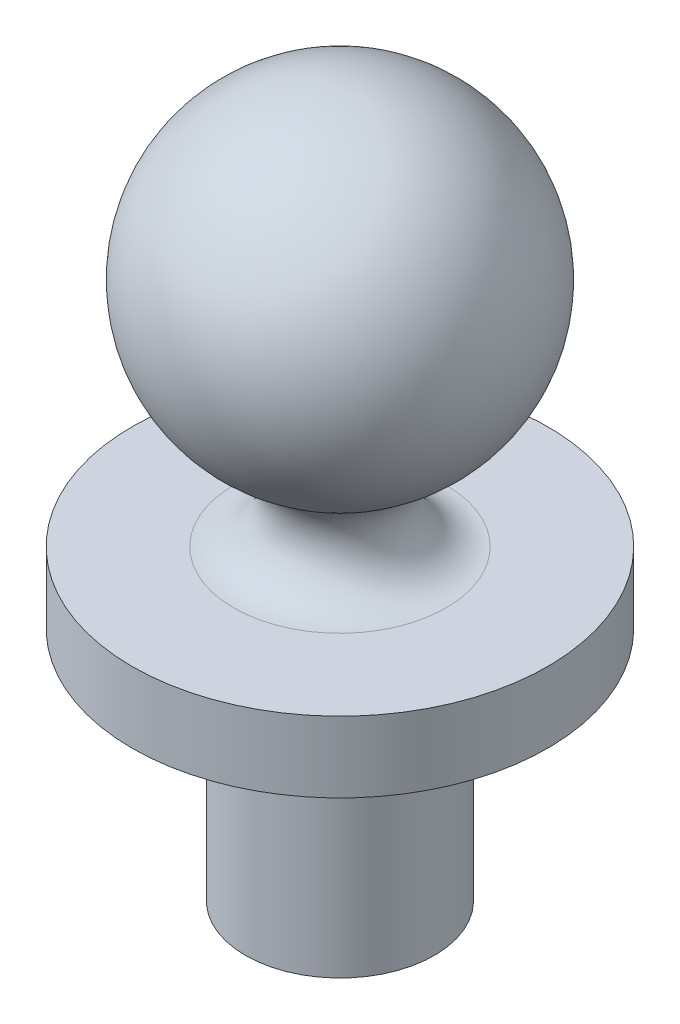
SolidWorks part; units mm, degrees
ref_plane "Front Plane" through (0, 0, 0) normal (0, 0, 1) x (1, 0, 0)
ref_plane "Top Plane" through (0, 0, 0) normal (0, 1, 0) x (1, 0, 0)
ref_plane "Right Plane" through (0, 0, 0) normal (1, 0, 0) x (0, 0, -1)
sketch "Sketch1" plane through (0, 0, 0) normal (0, 0, 1) x (1, 0, 0)
  line L0 (0, 40.4201) -> (0, -33.5359) construction
  line L1 (-1.125, -1.9486) -> (-0.875, -1.5155) construction
  line L2 (-0.875, -1.5155) -> (-1, -1.9821) construction
  line L3 (-1, -1.9821) -> (-1.125, -1.9486) construction
  line L4 (-1.125, -2.4486) -> (-2.2, -2.4486)
  line L5 (-2.2, -2.4486) -> (-2.2, -3.1986)
  line L6 (-2.2, -3.1986) -> (-1, -3.1986)
  line L7 (-1, -3.1986) -> (-1, -5.6986)
  line L8 (-1, -5.6986) -> (0, -5.6986)
  line L9 (0, -5.6986) -> (0, -1.75)
  line L10 (0, 1.75) -> (0, -1.75)
  line L11 (-1, -1.9821) -> (-1.125, -2.4486) construction
  line L12 (-1.125, -1.9486) -> (-1.125, -2.4486) construction
  arc A0 (0, -1.75) -> (0, 1.75) centre (0, 0) cw
  arc A1 (-0.875, -1.5155) -> (-1.125, -2.4486) centre (-1.125, -1.9486) cw
  dimension "D3" = 0.5
  dimension "D5" = 1.75
  dimension "D1" = 1
  dimension "D2" = 2.2
  dimension "D4" = 150
  dimension "D6" = 2.5
  dimension "D7" = 0.75
revolve "Revolve1" add sketch "Sketch1" angle 360 about L0
